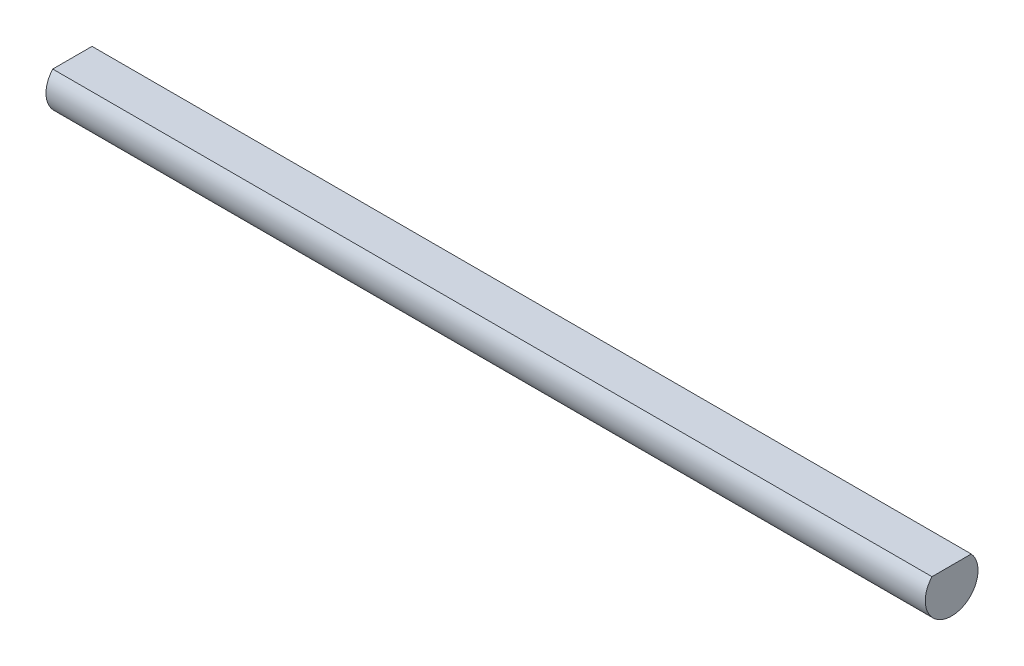
SolidWorks part; units mm, degrees
material "Plain Carbon Steel"
ref_plane "Front Plane" through (0, 0, 0) normal (0, 0, 1) x (1, 0, 0)
ref_plane "Top Plane" through (0, 0, 0) normal (0, 1, 0) x (1, 0, 0)
ref_plane "Right Plane" through (0, 0, 0) normal (1, 0, 0) x (0, 0, -1)
sketch "Sketch1" plane through (0, 0, 0) normal (1, 0, 0) x (0, 0, -1)
  line L0 (-2.2361, 2) -> (2.2361, 2)
  arc A0 (-2.2361, 2) -> (2.2361, 2) centre (0, 0) ccw
  dimension "D1" = 6
  dimension "D2" = 2
extrude "Boss-Extrude1" add sketch "Sketch1" along normal mid plane 100
